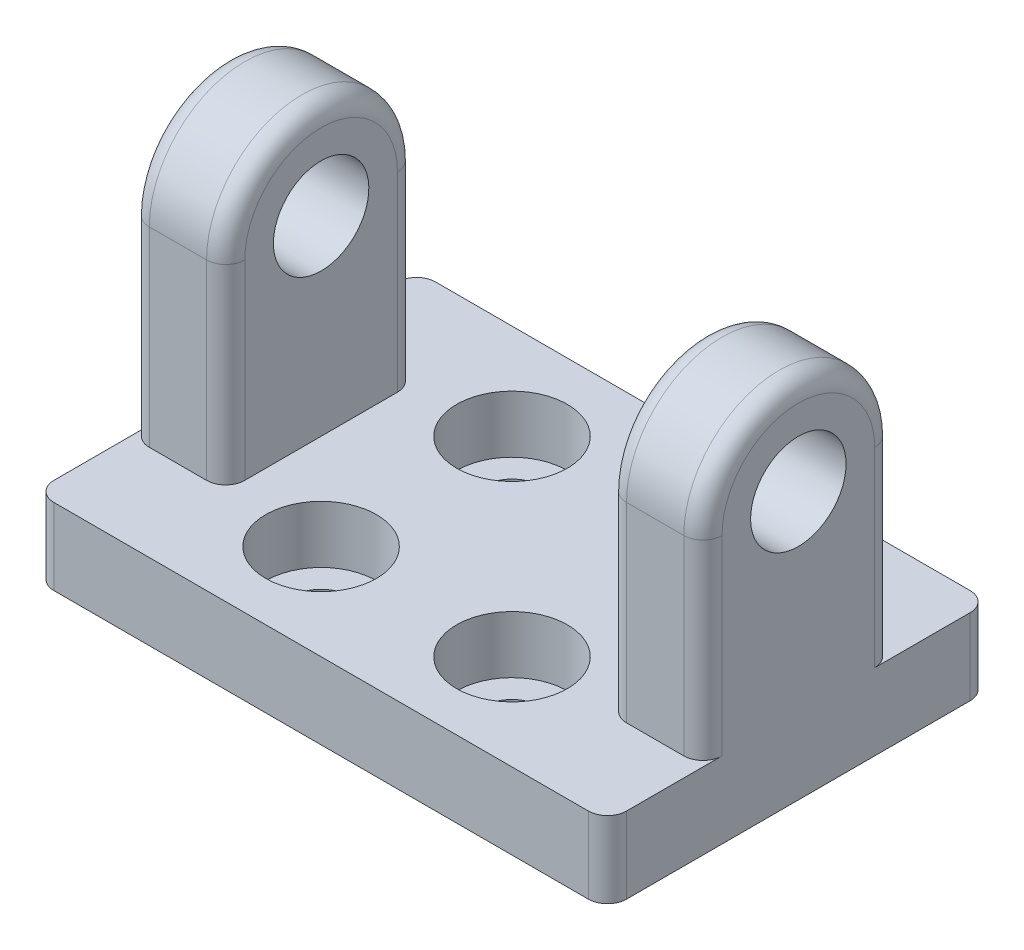
SolidWorks part; units mm, degrees
ref_plane "Plan de face" through (0, 0, 0) normal (0, 0, 1) x (1, 0, 0)
ref_plane "Plan de dessus" through (0, 0, 0) normal (0, 1, 0) x (1, 0, 0)
ref_plane "Plan de droite" through (0, 0, 0) normal (1, 0, 0) x (0, 0, -1)
sketch "Esquisse2" plane through (0, 0, 0) normal (1, 0, 0) x (0, 0, -1)
  line L0 (5, 0) -> (5, -10)
  line L2 (-5, 0) -> (-5, -10)
  line L3 (-5, -10) -> (5, -10)
  circle A0 centre (0, 0) radius 2.5
  arc A2 (5, 0) -> (-5, 0) centre (0, 0) ccw
  dimension "D1" = 5
  dimension "D2" = 10
  dimension "D3" = 5
  dimension "D4" = 5
extrude "Boss.-Extru.1" add sketch "Esquisse2" along normal mid plane 30
sketch "Esquisse4" plane through (0, -10, 0) normal (0, -1, 0) x (1, 0, 0)
  line L0 (-15, 5) -> (-15, -5) construction
  line L1 (-15, -10) -> (15, -10)
  line L2 (-15, -10) -> (-15, 10)
  line L3 (-15, 10) -> (15, 10)
  line L4 (15, -10) -> (15, 10)
  line L5 (15, 5) -> (15, -5) construction
  dimension "D1" = 20
  dimension "D4" = 10
extrude "Boss.-Extru.2" add sketch "Esquisse4" along normal blind 4
sketch "Esquisse5" plane through (0, -10, 0) normal (0, 1, 0) x (1, 0, 0)
  circle A0 centre (5, -5) radius 1.5
  circle A1 centre (5, 5) radius 1.5
  circle A2 centre (-5, 5) radius 1.5
  circle A3 centre (-5, -5) radius 1.5
  point P15 (0, 0)
  dimension "D1" = 3
  dimension "D2" = 10
  dimension "D3" = 10
  dimension "D4" = 5
  dimension "D5" = 5
extrude "Enlèv. mat.-Extru.1" cut sketch "Esquisse5" against normal up to next contours A0
sketch "Esquisse6" plane through (0, 0, 5) normal (0, 0, 1) x (1, 0, 0)
  line L0 (15, -10) -> (6.5, -10) construction
  line L1 (-10, 11.5437) -> (10, 11.5437)
  line L2 (-10, 11.5437) -> (-10, -10)
  line L3 (-10, -10) -> (10, -10)
  line L4 (10, 11.5437) -> (10, -10)
  line L5 (15, 0) -> (-15, 0) construction
  point P7 (0, 11.5437)
  point P11 (0, 0)
  dimension "D2" = 20
extrude "Enlèv. mat.-Extru.2" cut sketch "Esquisse6" against normal through all
sketch "Esquisse7" plane through (0, -10, 0) normal (0, 1, 0) x (1, 0, 0)
  circle A4 centre (-5, 5) radius 2.9
  circle A5 centre (5, 5) radius 2.9
  circle A6 centre (5, -5) radius 2.9
  circle A7 centre (-5, -5) radius 2.9
  dimension "D1" = 5.8
extrude "Enlèv. mat.-Extru.3" cut sketch "Esquisse7" against normal blind 3
fillet "Congé1" radius 1 16 edges at (10, -5, -5) (10, -5, 5) (-10, -5, 5) (-10, -5, -5) (15, -5, -5) (15, -5, 5) (-15, -5, -5) (-15, -5, 5) (10, 5, 0) (-10, 5, 0) (15, 5, 0) (-15, 5, 0) (-15, -12, -10) (-15, -12, 10) (15, -12, -10) (15, -12, 10)
